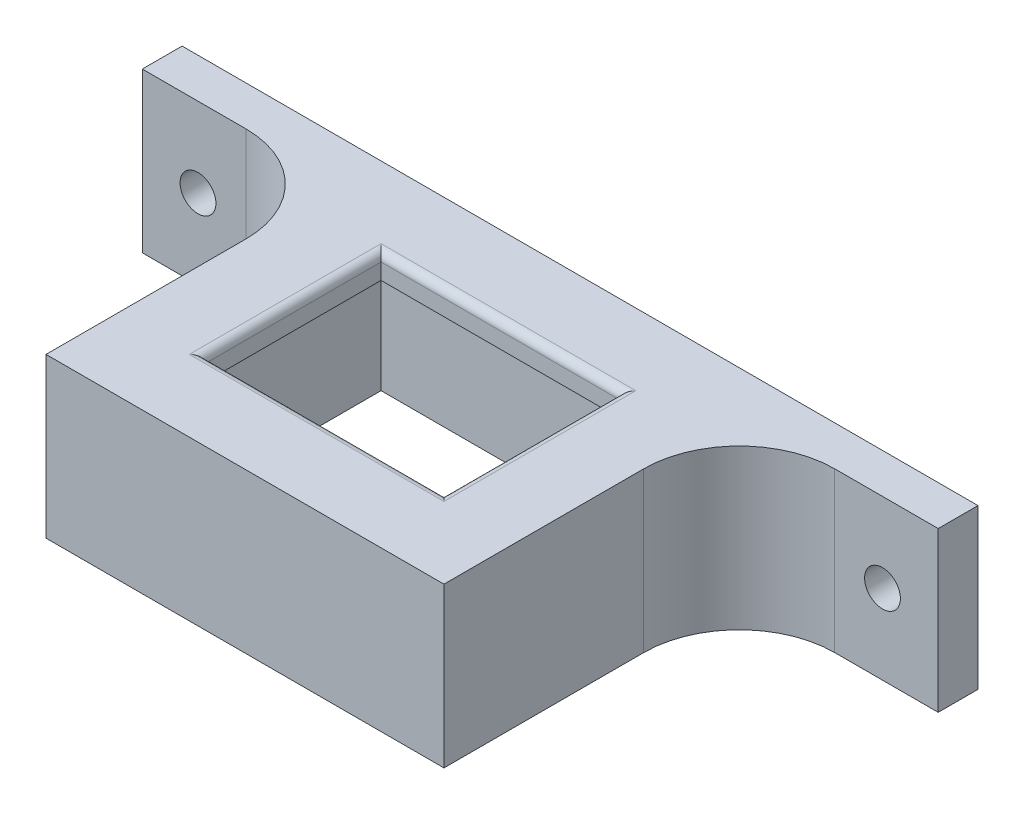
SolidWorks part; units mm, degrees
ref_plane "Front Plane" through (0, 0, 0) normal (0, 0, 1) x (1, 0, 0)
ref_plane "Top Plane" through (0, 0, 0) normal (0, 1, 0) x (1, 0, 0)
ref_plane "Right Plane" through (0, 0, 0) normal (1, 0, 0) x (0, 0, -1)
sketch "Sketch1" plane through (0, 0, 0) normal (0, 1, 0) x (1, 0, 0)
  line L0 (-25, -21.05) -> (-25, 21.05)
  line L1 (-15, -11.05) -> (15, -11.05)
  line L2 (-15, -11.05) -> (-15, 11.05)
  line L3 (-15, 11.05) -> (15, 11.05)
  line L4 (15, -11.05) -> (15, 11.05)
  line L5 (-15, -11.05) -> (15, 11.05) construction
  line L6 (-15, 11.05) -> (15, -11.05) construction
  line L7 (-25, 21.05) -> (25, 21.05)
  line L8 (25, -21.05) -> (25, 21.05)
  line L9 (-25, -21.05) -> (25, -21.05)
  point P0 (0, 0)
  dimension "D1" = 30
  dimension "D2" = 22.1
  dimension "D3" = 10
extrude "Boss-Extrude2" add sketch "Sketch1" against normal blind 3
fillet "Fillet1" radius 1 4 edges at (0, 0, 11.05) (15, 0, 0) (0, 0, -11.05) (-15, 0, 0)
sketch "Sketch2" plane through (0, -3, 0) normal (0, -1, 0) x (1, 0, 0)
  line L0 (-20, -16.05) -> (-20, 16.05)
  line L1 (25, -21.05) -> (-25, -21.05)
  line L2 (25, -21.05) -> (25, 21.05)
  line L3 (25, 21.05) -> (-25, 21.05)
  line L4 (-25, -21.05) -> (-25, 21.05)
  line L5 (25, -21.05) -> (-25, 21.05) construction
  line L6 (25, 21.05) -> (-25, -21.05) construction
  line L7 (20, 16.05) -> (-20, 16.05)
  line L8 (20, -16.05) -> (20, 16.05)
  line L9 (20, -16.05) -> (-20, -16.05)
  point P0 (0, 0)
  dimension "D1" = 5
extrude "Boss-Extrude3" add sketch "Sketch2" along normal blind 17
sketch "Sketch3" plane through (0, 0, -21.05) normal (0, 0, -1) x (-1, 0, 0)
  line L0 (23.155, 0) -> (-23.155, 0) construction
  line L1 (-25, 0) -> (-50, 0)
  line L2 (-25, 0) -> (-25, -20)
  line L3 (-25, -20) -> (-50, -20)
  line L4 (-50, 0) -> (-50, -20)
  line L5 (-25, -20) -> (-25, 0) construction
  line L6 (25, -20) -> (-25, -20) construction
  line L7 (-43, -20) -> (-43, 0) construction
  point P12 (-43, -10)
  dimension "D1" = 25
  dimension "D2" = 7
extrude "Boss-Extrude4" add sketch "Sketch3" against normal up to surface (5 mm away) up to face at (0, -11.5, -16.05)
hole_wizard "M4 Clearance Hole1" positions "3DSketch1" profile "Sketch6" hole size "M4" standard "ISO" end condition through all
sketch3d "3DSketch1"
  point P0 (43, -10, -21.05)
sketch "Sketch6" plane through (43, -10, -21.05) normal (1, 0, 0) x (0, 1, 0)
  line L0 (0, 0) -> (0, 42.1)
  line L1 (0, 42.1) -> (2.25, 42.1)
  line L2 (2.25, 42.1) -> (2.25, 0.025)
  line L3 (2.25, 0.025) -> (2.275, 0)
  line L5 (2.275, 0) -> (0, 0)
  line L6 (-2.25, 0.025) -> (-2.275, 0) construction
  line L11 (0, -6.35) -> (0, 107.95) construction
  dimension "Thru Hole Dia." = 4.5
  dimension "Thru Hole Depth" = 42.1
  dimension "Near C'Sink Dia." = 4.55
  dimension "Near C'Sink Angle" = 90
mirror "Mirror4" about plane through (0, 0, 0) normal (1, 0, 0) of "M4 Clearance Hole1", "Boss-Extrude4"
fillet "Fillet2" radius 12 2 edges at (25, -10, -16.05) (-25, -10, -16.05)
